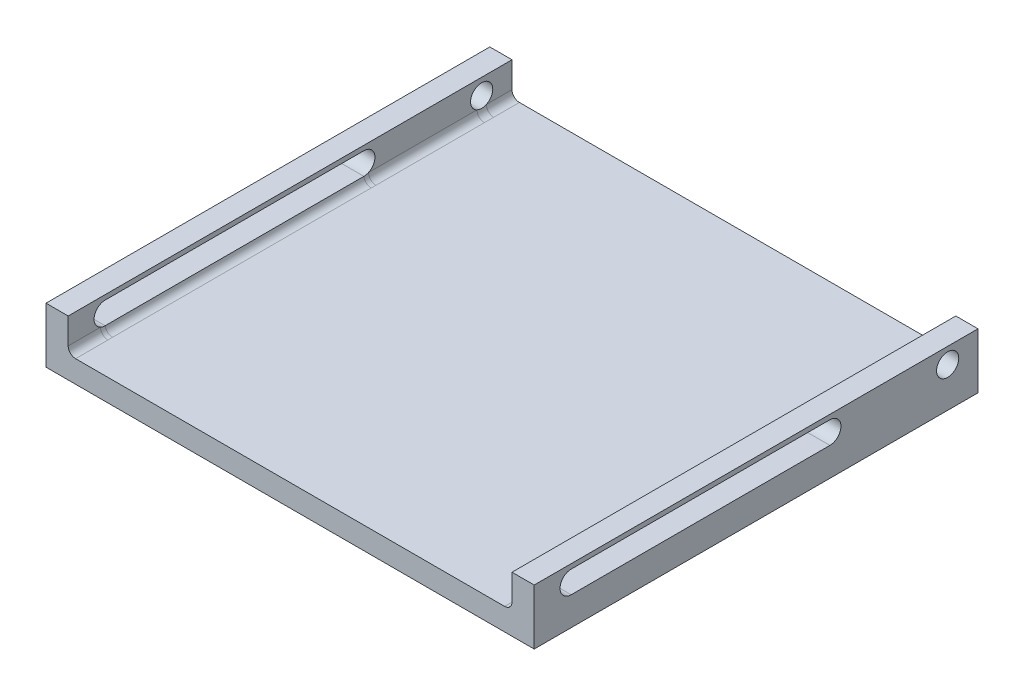
SolidWorks part; units mm, degrees
material "7079 Alloy"
ref_plane "Front Plane" through (0, 0, 0) normal (0, 0, 1) x (1, 0, 0)
ref_plane "Top Plane" through (0, 0, 0) normal (0, 1, 0) x (1, 0, 0)
ref_plane "Right Plane" through (0, 0, 0) normal (1, 0, 0) x (0, 0, -1)
sketch "Sketch1" plane through (0, 0, 0) normal (0, 1, 0) x (1, 0, 0)
  line L1 (-300, 300) -> (300, 300)
  line L2 (-300, 300) -> (-300, -300)
  line L3 (-300, -300) -> (300, -300)
  line L4 (300, 300) -> (300, -300)
  line L5 (-300, 300) -> (300, -300) construction
  line L6 (-300, -300) -> (300, 300) construction
  point P0 (0, 0)
extrude "Boss-Extrude1" add sketch "Sketch1" along normal blind 30
sketch "Sketch2" plane through (300, 0, 0) normal (1, 0, 0) x (0, 0, -1)
  line L1 (-300, 0) -> (300, 0)
  line L2 (-300, 0) -> (-300, 75)
  line L3 (-300, 75) -> (300, 75)
  line L4 (300, 0) -> (300, 75)
  circle A0 centre (258.9934, 53.6077) radius 15
  dimension "D1" = 30
extrude "Boss-Extrude2" add sketch "Sketch2" along normal blind 30
sketch "Sketch3" plane through (330, 0, 0) normal (1, 0, 0) x (0, 0, -1)
  line L0 (-250, 53.6077) -> (99.7366, 53.6077) construction
  line L1 (-250, 68.6077) -> (99.7366, 68.6077)
  line L2 (-250, 38.6077) -> (99.7366, 38.6077)
  line L3 (-300, 75) -> (-300, 0) construction
  arc A0 (-250, 68.6077) -> (-250, 38.6077) centre (-250, 53.6077) ccw
  arc A1 (99.7366, 38.6077) -> (99.7366, 68.6077) centre (99.7366, 53.6077) ccw
  point P3 (-75.1317, 53.6077)
  dimension "D1" = 30
  dimension "D2" = 50
extrude "Cut-Extrude4" cut sketch "Sketch3" along direction (-1, 0, 0) on the side of the normal blind 30 and the other way through all
mirror "Mirror1" about plane through (0, 0, 0) normal (1, 0, 0) of "Cut-Extrude4", "Boss-Extrude2"
fillet "Fillet1" radius 10 2 edges
